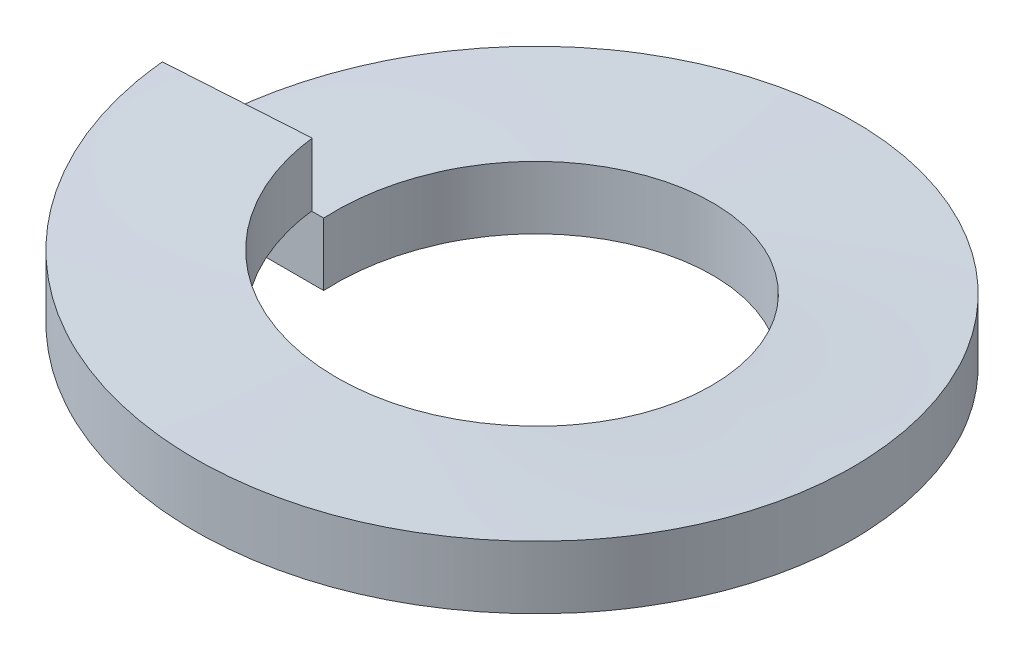
SolidWorks part; units mm, degrees
ref_plane "Front Plane" through (0, 0, 0) normal (0, 0, 1) x (1, 0, 0)
ref_plane "Top Plane" through (0, 0, 0) normal (0, 1, 0) x (1, 0, 0)
ref_plane "Right Plane" through (0, 0, 0) normal (1, 0, 0) x (0, 0, -1)
sketch "Sketch1" plane through (0, 0, 0) normal (0, 0, 1) x (1, 0, 0)
  line L0 (0, 0) -> (0, 0.508) construction
  line L1 (-2.667, 0.508) -> (-1.524, 0.508)
  line L2 (-2.667, 0.508) -> (-2.667, 0)
  line L3 (-2.667, 0) -> (-1.524, 0)
  line L4 (-1.524, 0.508) -> (-1.524, 0)
  dimension "ID" = 3.048
  dimension "OD" = 5.334
  dimension "Min Thickness" = 0.508
sketch "Sketch2" plane through (0, 0, 0) normal (0, 1, 0) x (1, 0, 0)
  circle A0 centre (0, 0) radius 2.667
curve "Helix/Spiral1" pitch 0.6158 height 0.6096 turns 0.99
sweep "Sweep1" add profiles "Sketch1" path "Helix/Spiral1"
ref_plane "Plane1" through (0, 0.254, 0) normal (0, 1, 0) x (-1, 0, 0)
sketch "Sketch3" plane through (0, 0.254, 0) normal (0, 1, 0) x (1, 0, 0)
  circle A0 centre (0, 0) radius 1.524
  circle A1 centre (0, 0) radius 2.667
  point P4 (0, 1.524)
equation "\"D3@Helix/Spiral1\" = \"Min Thickness@Sketch1\"*1.2"
equation "\"D1@Plane1\" = \"Min Thickness@Sketch1\"/2"
